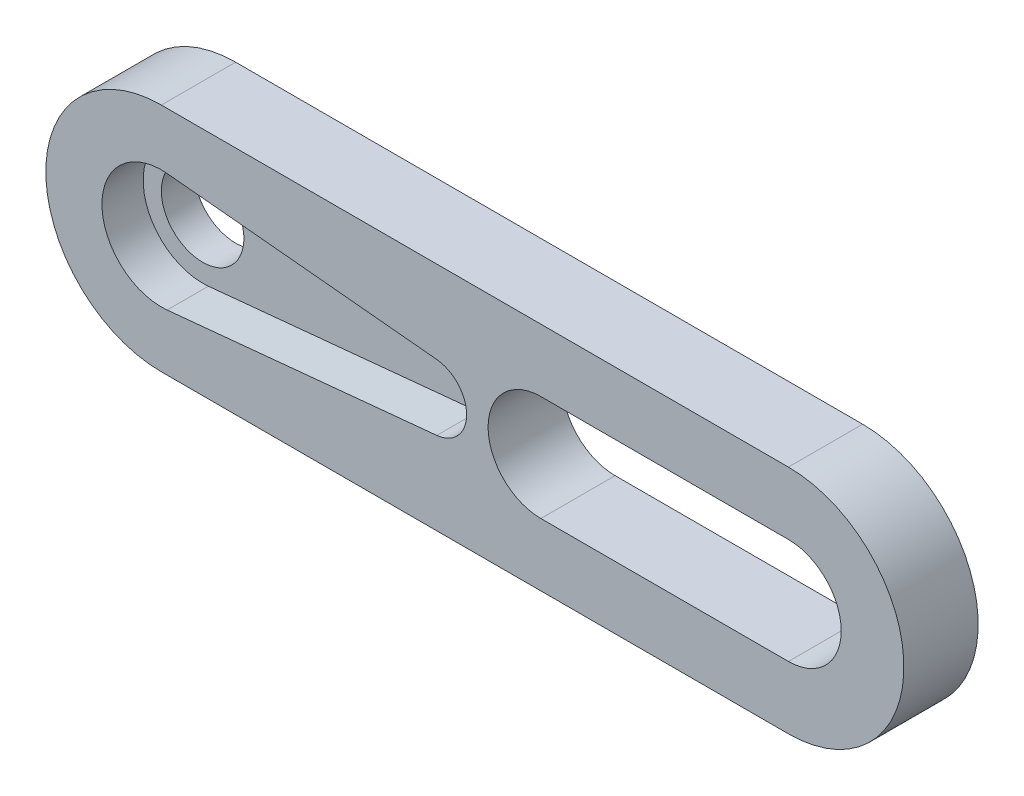
SolidWorks part; units mm, degrees
ref_plane "Front Plane" through (0, 0, 0) normal (0, 0, 1) x (1, 0, 0)
ref_plane "Top Plane" through (0, 0, 0) normal (0, 1, 0) x (1, 0, 0)
ref_plane "Right Plane" through (0, 0, 0) normal (1, 0, 0) x (0, 0, -1)
sketch "Esquisse1" plane through (0, 0, 0) normal (0, 0, 1) x (1, 0, 0)
  line L0 (-3.6, 0) -> (-3.6, 5.3986) construction
  line L1 (0.3491, 3.583) -> (16.6939, 1.9906)
  line L2 (16.6939, -1.9906) -> (0.3491, -3.583)
  line L3 (18.5, 0) -> (18.5, 4.9554) construction
  line L4 (0, 7) -> (38, 7)
  line L5 (0, -7) -> (38, -7)
  line L6 (23, 0) -> (38, 0) construction
  line L7 (23, 3.2) -> (38, 3.2)
  line L8 (23, -3.2) -> (38, -3.2)
  arc A0 (0.3491, 3.583) -> (0.3491, -3.583) centre (0, 0) ccw
  arc A1 (16.6939, -1.9906) -> (16.6939, 1.9906) centre (16.5, 0) ccw
  arc A2 (23, 3.2) -> (23, -3.2) centre (23, 0) ccw
  arc A3 (0, -7) -> (0, 7) centre (0, 0) cw
  arc A4 (38, 7) -> (38, -7) centre (38, 0) cw
  arc A5 (38, -3.2) -> (38, 3.2) centre (38, 0) ccw
  point P15 (30.5, 0)
  dimension "D2" = 3.6
  dimension "D3" = 2
  dimension "D5" = 15
  dimension "D6" = 7
  dimension "D8" = 7
  dimension "D4" = 3.2
  dimension "D1" = 22.1
  dimension "D7" = 38
extrude "Main" add sketch "Esquisse1" along normal blind 2.5
sketch "Esquisse2" plane through (0, 0, 0) normal (0, 0, -1) x (-1, 0, 0)
  line L0 (0, -7) -> (-38, -7)
  line L1 (0, -7) -> (-38, -7) construction
  line L2 (0, -7) -> (-38, -7) construction
  line L3 (0, 7) -> (-38, 7)
  arc A0 (-38, 7) -> (-38, -7) centre (-38, 0) ccw construction
  circle A2 centre (0, 0) radius 2.5
  arc A3 (0, -7) -> (0, 7) centre (0, 0) ccw
  arc A5 (-38, 7) -> (-38, -7) centre (-38, 0) ccw
  dimension "D1" = 5
extrude "OriginalBracket" add sketch "Esquisse2" along normal blind 2
sketch "Sketch1" plane through (0, 0, 0) normal (0, 0, 1) x (1, 0, 0)
  line L0 (23, 0) -> (38, 0) construction
  line L1 (23, 3.2) -> (38, 3.2)
  line L2 (23, -3.2) -> (38, -3.2)
  arc A0 (23, 3.2) -> (23, -3.2) centre (23, 0) ccw
  arc A1 (38, -3.2) -> (38, 3.2) centre (38, 0) ccw
  point P4 (30.5, 0)
extrude "Cut-Extrude1" cut sketch "Sketch1" against normal through all
